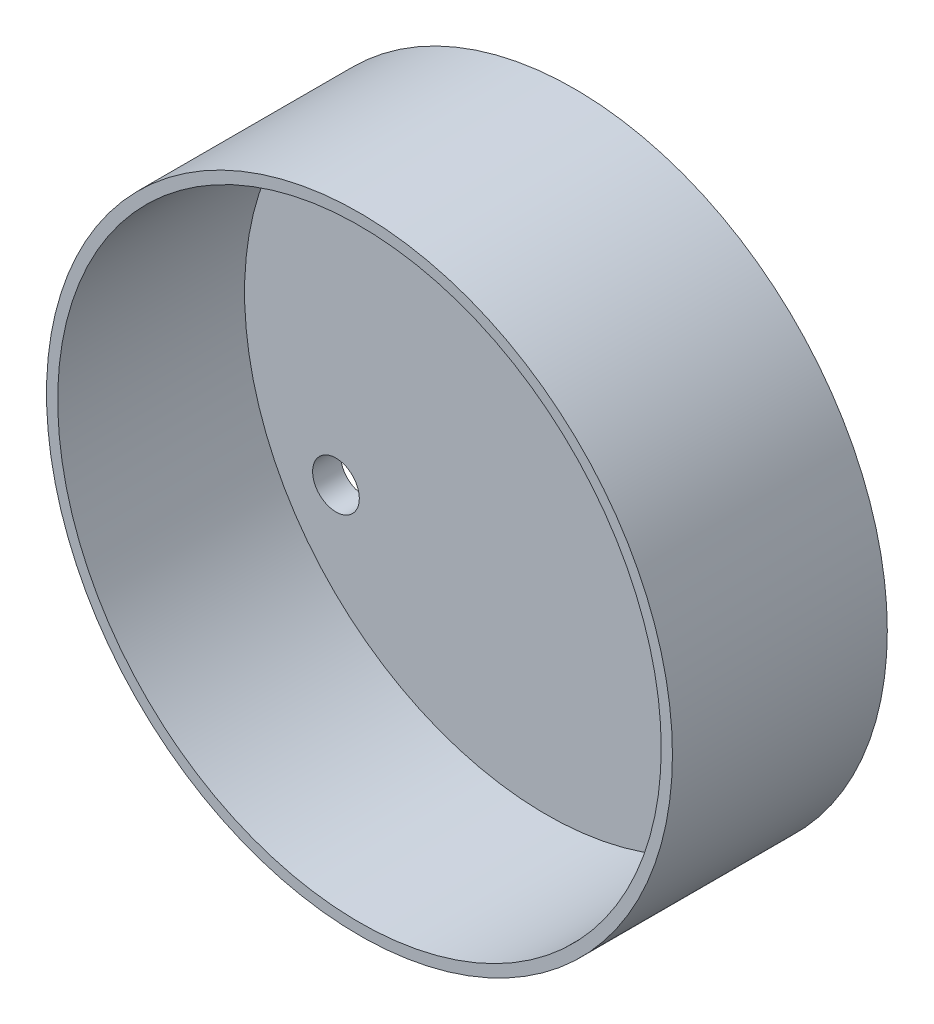
SolidWorks part; units mm, degrees
ref_plane "前视基准面" through (0, 0, 0) normal (0, 0, 1) x (1, 0, 0)
ref_plane "上视基准面" through (0, 0, 0) normal (0, 1, 0) x (1, 0, 0)
ref_plane "右视基准面" through (0, 0, 0) normal (1, 0, 0) x (0, 0, -1)
sketch "草图1" plane through (0, 0, 0) normal (0, 0, 1) x (1, 0, 0)
  circle A0 centre (0, 0) radius 13 construction
  circle A1 centre (0, 13) radius 1.25
  circle A2 centre (11.2583, -6.5) radius 1.25
  circle A3 centre (-11.2583, -6.5) radius 1.25
  circle A4 centre (0, 0) radius 16.75
  point P11 (0, 0)
  dimension "D1" = 26
  dimension "D2" = 2.5
  dimension "D7" = 33.5
  dimension "D4" = 120
  dimension "D5" = 11.2583
  dimension "D6" = 6.5
  dimension "D3" = 3
extrude "凸台-拉伸1" add sketch "草图1" along normal blind 1.5
sketch "草图2" plane through (0, 0, 1.5) normal (0, 0, 1) x (1, 0, 0)
  circle A0 centre (0, 0) radius 16.75
  circle A1 centre (0, 0) radius 16.75 construction
  circle A2 centre (0, 0) radius 16.15
  dimension "D1" = 32.3
extrude "凸台-拉伸2" add sketch "草图2" along normal blind 10
